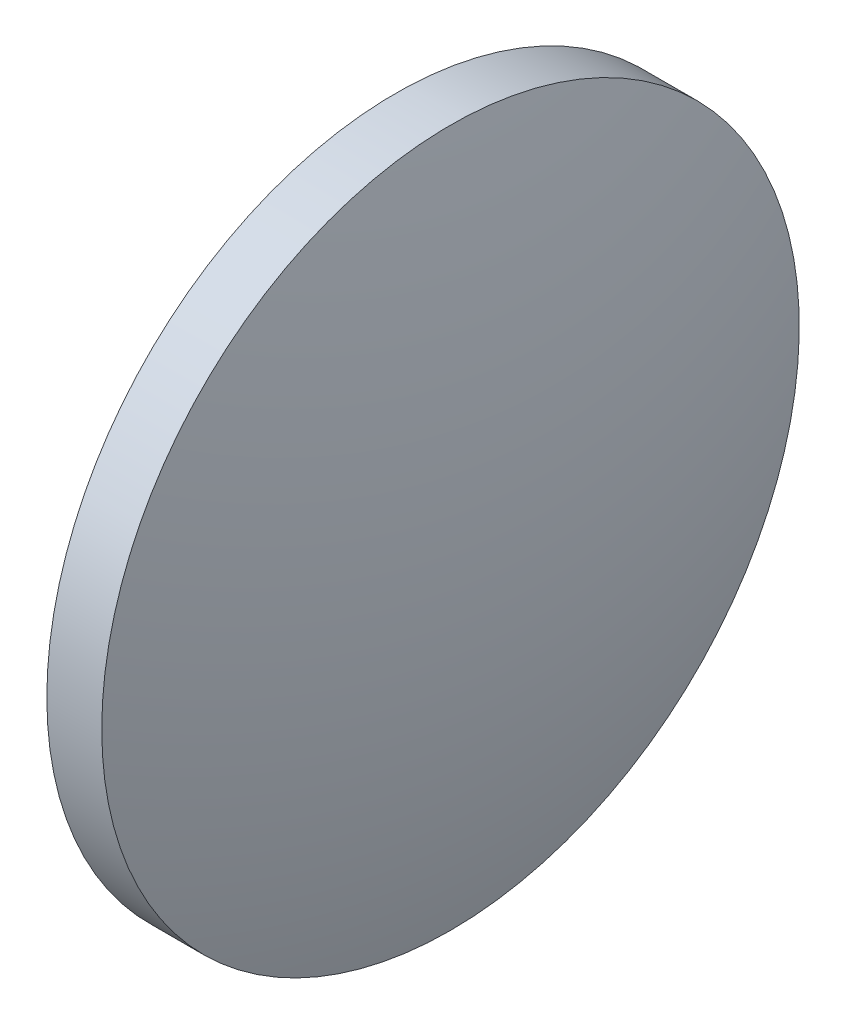
SolidWorks part; units mm, degrees
ref_plane "前视基准面" through (0, 0, 0) normal (0, 0, 1) x (1, 0, 0)
ref_plane "上视基准面" through (0, 0, 0) normal (0, 1, 0) x (1, 0, 0)
ref_plane "右视基准面" through (0, 0, 0) normal (1, 0, 0) x (0, 0, -1)
sketch "草图1" plane through (0, 0, 0) normal (0, 0, 1) x (1, 0, 0)
  line L0 (522.6446, 102.4595) -> (541.4406, 102.4595) construction
  line L1 (528.3829, 102.4595) -> (528.3829, 115.1595)
  line L2 (528.3829, 115.1595) -> (530.3829, 115.1595)
  line L3 (532.2829, 102.4595) -> (528.3829, 102.4595)
  arc A0 (532.2829, 102.4595) -> (530.3829, 115.1595) centre (488.8881, 102.4595) ccw
revolve "旋转1" add sketch "草图1" angle 360 about L0
